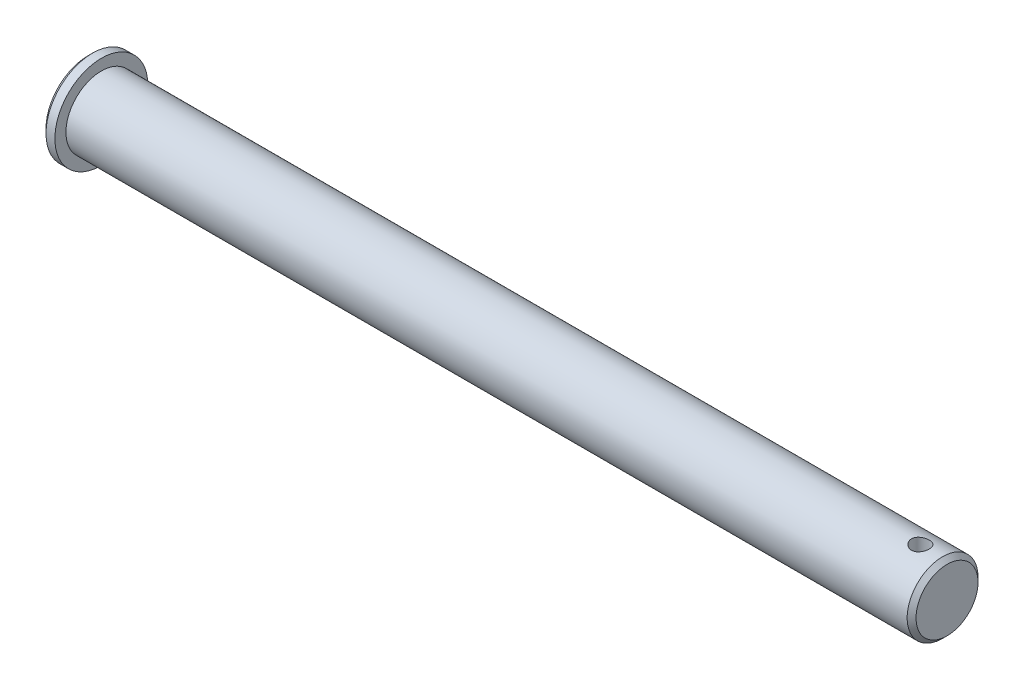
SolidWorks part; units mm, degrees
ref_plane "Płaszczyzna przednia" through (0, 0, 0) normal (0, 0, 1) x (1, 0, 0)
ref_plane "Płaszczyzna górna" through (0, 0, 0) normal (0, 1, 0) x (1, 0, 0)
ref_plane "Płaszczyzna prawa" through (0, 0, 0) normal (1, 0, 0) x (0, 0, -1)
sketch "Szkic1" plane through (0, 0, 0) normal (0, 0, 1) x (1, 0, 0)
  line L0 (0, 0) -> (0, 10.5)
  line L1 (0, 10.5) -> (3, 10.5)
  line L2 (3, 10.5) -> (3, 8)
  line L3 (3, 8) -> (194, 8)
  line L4 (194, 8) -> (194, 0)
  line L5 (194, 0) -> (0, 0)
  dimension "D1" = 3
  dimension "D2" = 10.5
  dimension "D3" = 8
  dimension "D4" = 191
revolve "Obrót1" add sketch "Szkic1" angle 360 about L5
sketch "Szkic2" plane through (0, 0, 0) normal (0, 1, 0) x (1, 0, 0)
  line L0 (0, 0) -> (188, 0) construction
  circle A0 centre (188, 0) radius 2
  dimension "D1" = 188
extrude "Wytnij-wyciągnięcie1" cut sketch "Szkic2" against normal through all and the other way through all
chamfer "Sfazowanie1" distance 1 angle 45 2 edges at (194, 0, -8) (0, 0, -10.5)
